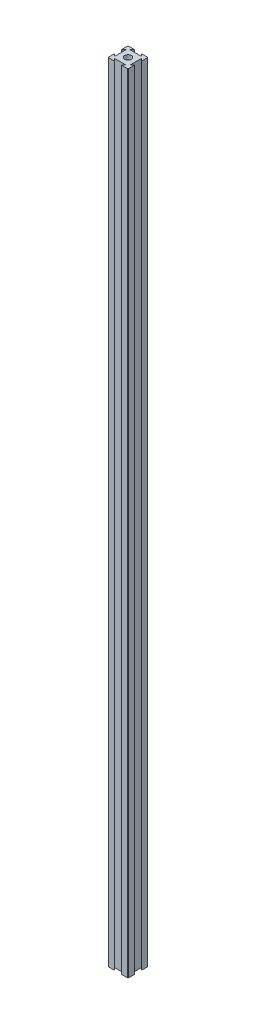
SolidWorks part; units mm, degrees
material "Alumina"
ref_plane "Front Plane" through (0, 0, 0) normal (0, 0, 1) x (1, 0, 0)
ref_plane "Top Plane" through (0, 0, 0) normal (0, 1, 0) x (1, 0, 0)
ref_plane "Right Plane" through (0, 0, 0) normal (1, 0, 0) x (0, 0, -1)
sketch "Sketch1" plane through (0, 0, 0) normal (0, 1, 0) x (1, 0, 0)
  line L0 (6.6667, 20) -> (4.285, 17.6183)
  line L1 (0, 0) -> (20, 0)
  line L2 (0, 0) -> (0, 20)
  line L3 (0, 20) -> (20, 20)
  line L4 (20, 0) -> (20, 20)
  line L5 (4.285, 17.6183) -> (15.715, 17.6183)
  line L6 (15.715, 17.6183) -> (13.3333, 20)
  line L7 (13.3333, 20) -> (6.6667, 20)
  line L8 (0, 10) -> (20, 10) construction
  line L9 (10, 20) -> (10, 0) construction
  line L10 (15.715, 2.3817) -> (13.3333, 0)
  line L11 (4.285, 2.3817) -> (15.715, 2.3817)
  line L12 (6.6667, 0) -> (4.285, 2.3817)
  line L13 (13.3333, 0) -> (6.6667, 0)
  line L14 (0, 13.3333) -> (2.3817, 15.715)
  line L15 (2.3817, 15.715) -> (2.3817, 4.285)
  line L16 (2.3817, 4.285) -> (0, 6.6667)
  line L17 (0, 6.6667) -> (0, 13.3333)
  line L18 (17.6183, 4.285) -> (20, 6.6667)
  line L19 (17.6183, 15.715) -> (17.6183, 4.285)
  line L20 (20, 13.3333) -> (17.6183, 15.715)
  line L21 (20, 6.6667) -> (20, 13.3333)
  circle A0 centre (10, 10) radius 3.3333
  dimension "D1" = 20
  dimension "D2" = 20
  dimension "D3" = 6.6667
  dimension "D4" = 6.6667
  dimension "D5" = 45
  dimension "D6" = 45
  dimension "D7" = 11.43
  dimension "D8" = 6.6667
  dimension "D9" = 6.6667
  dimension "D10" = 11.43
  dimension "D11" = 45
  dimension "D12" = 45
extrude "Boss-Extrude1" add sketch "Sketch1" along normal blind 787.4 contours L20 L4 L3 L6 L5 L0 L2 L14 L15 L16 L1 L12 L11 L10 L18 L19 A0
fillet "Fillet4" radius 0.508 4 edges at (0, 393.7, -20) (20, 393.7, -20) (0, 393.7, 0) (20, 393.7, 0)
